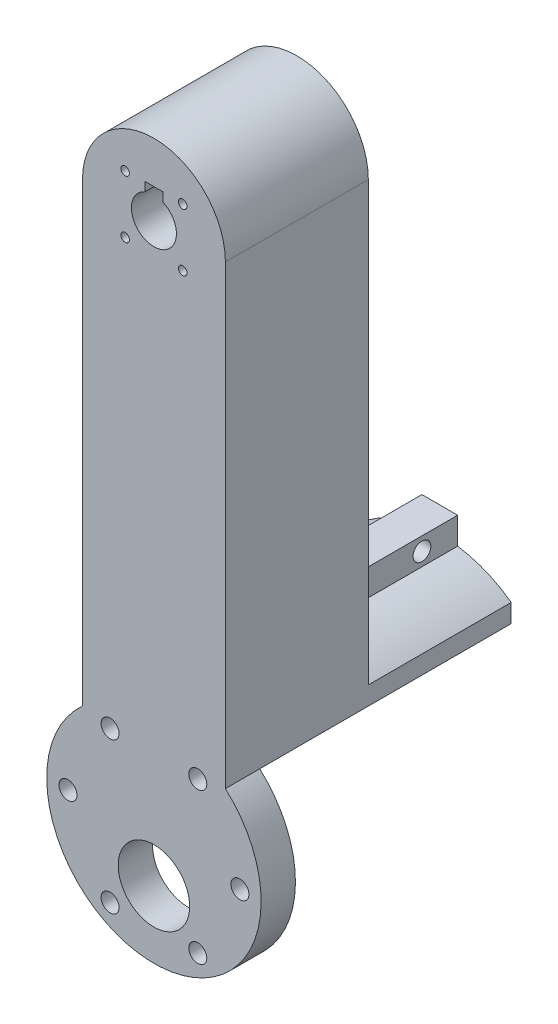
SolidWorks part; units mm, degrees
ref_plane "Front Plane" through (0, 0, 0) normal (0, 0, 1) x (1, 0, 0)
ref_plane "Top Plane" through (0, 0, 0) normal (0, 1, 0) x (1, 0, 0)
ref_plane "Right Plane" through (0, 0, 0) normal (1, 0, 0) x (0, 0, -1)
sketch "Sketch1" plane through (0, 0, 0) normal (0, 0, 1) x (1, 0, 0)
  line L0 (-5.1187, 55.9187) -> (5.1187, 45.6813) construction
  line L2 (12.7, 50.8) -> (12.7, -50.8)
  line L4 (-12.7, 50.8) -> (-12.7, -50.8)
  line L5 (12.7, 50.8) -> (-12.7, -50.8) construction
  line L6 (12.7, -50.8) -> (-12.7, 50.8) construction
  line L7 (5.1187, 55.9187) -> (-5.1187, 45.6813) construction
  line L8 (0, 50.8) -> (0, 51.7208) construction
  arc A0 (-12.7, 50.8) -> (12.7, 50.8) centre (0, 50.8) cw
  arc A1 (12.7, -50.8) -> (-12.7, -50.8) centre (0, -50.8) cw
  circle A2 centre (0, 50.8) radius 4
  circle A3 centre (-5.1187, 55.9187) radius 0.762
  circle A4 centre (5.1187, 55.9187) radius 0.762
  circle A5 centre (5.1187, 45.6813) radius 0.762
  circle A6 centre (-5.1187, 45.6813) radius 0.762
  point P0 (0, 0)
  point P14 (0, 50.8)
  point P15 (0, 50.8)
  dimension "D3" = 8
  dimension "D6" = 1.524
  dimension "D1" = 25.4
  dimension "D2" = 101.6
  dimension "D4" = 45
  dimension "D5" = 14.478
extrude "Boss-Extrude1" add sketch "Sketch1" along normal blind 25.4
sketch "Sketch2" plane through (0, 0, 0) normal (0, 0, -1) x (-1, 0, 0)
  circle A0 centre (0, -44.45) radius 19.05
  arc A2 (-12.7, -50.8) -> (12.7, -50.8) centre (0, -50.8) ccw construction
  dimension "D1" = 38.1
extrude "Boss-Extrude2" add sketch "Sketch2" against normal blind 25.4
sketch "Sketch4" plane through (0, 0, 25.4) normal (0, 0, 1) x (1, 0, 0)
  circle A0 centre (0, -44.45) radius 19.05
  arc A1 (-12.7, -30.251) -> (12.7, -30.251) centre (0, -44.45) ccw construction
  dimension "D1" = 38.1
sketch "Sketch5" plane through (0, 0, 25.4) normal (0, 0, 1) x (1, 0, 0)
  circle A0 centre (0, -51.562) radius 6.35
  dimension "D1" = 12.7
  dimension "D2" = 7.112
extrude "Cut-Extrude2" cut sketch "Sketch5" against normal blind 25.4
sketch "Sketch3" plane through (0, 0, 25.4) normal (0, 0, 1) x (1, 0, 0)
  circle A7 centre (15.2766, -44.45) radius 1.6 construction
  circle A8 centre (0, -44.45) radius 18.5
  circle A9 centre (0, -44.45) radius 18.5
  circle A10 centre (7.7942, -58.0175) radius 1.6 construction
  circle A11 centre (-7.7942, -58.0175) radius 1.6 construction
  circle A12 centre (-15.2766, -44.45) radius 1.6 construction
  circle A13 centre (7.7942, -31.2359) radius 1.6 construction
  circle A14 centre (-7.7942, -31.2359) radius 1.6 construction
  circle A15 centre (15.2766, -44.45) radius 1.6
  circle A16 centre (7.7942, -58.0175) radius 1.6
  circle A17 centre (-7.7942, -58.0175) radius 1.6
  circle A18 centre (-15.2766, -44.45) radius 1.6
  circle A19 centre (7.7942, -31.2359) radius 1.6
  circle A20 centre (-7.7942, -31.2359) radius 1.6
  dimension "D1" = 0
extrude "Cut-Extrude1" cut sketch "Sketch3" against normal blind 25.4 contours A20 | A18 | A15 | A17 | A19 | A16
sketch "Sketch6" plane through (0, 0, 0) normal (0, 0, -1) x (-1, 0, 0)
  line L1 (-1.5875, 56.059) -> (1.5875, 56.059)
  line L2 (-1.5875, 56.059) -> (-1.5875, 54.4715)
  line L3 (-1.5875, 54.4715) -> (1.5875, 54.4715)
  line L4 (1.5875, 56.059) -> (1.5875, 54.4715)
  circle A0 centre (0, 50.8) radius 4 construction
  dimension "D1" = 3.175
  dimension "D2" = 1.5875
extrude "Cut-Extrude3" cut sketch "Sketch6" against normal blind 25.4
sketch "Sketch8" plane through (0, 0, 0) normal (0, 0, -1) x (-1, 0, 0)
  circle A0 centre (0, -44.45) radius 19.05
  dimension "D1" = 38.1
extrude "Cut-Extrude4" cut sketch "Sketch8" against normal blind 19.3
sketch "Sketch9" plane through (0, 0, 0) normal (0, 0, -1) x (-1, 0, 0)
  line L0 (12.7, 50.8) -> (12.7, -30.251) construction
  line L1 (-12.7, -30.251) -> (-12.7, 50.8) construction
  line L2 (-12.7, -30.251) -> (-12.7, -26.9904)
  line L3 (12.7, -30.251) -> (12.7, -26.9904)
  arc A0 (-12.7, -30.251) -> (12.7, -30.251) centre (0, -44.45) cw
  arc A1 (-12.7, -26.9904) -> (12.7, -26.9904) centre (0, -44.45) cw
  dimension "D1" = 2.54
extrude "Boss-Extrude3" add sketch "Sketch9" along normal blind 25.4
sketch "Sketch10" plane through (0, 0, 0) normal (0, 0, -1) x (-1, 0, 0)
  line L1 (-3.175, -18.3322) -> (3.175, -18.3322)
  line L2 (-3.175, -18.3322) -> (-3.175, -23.0947)
  line L3 (-3.175, -23.0947) -> (3.175, -23.0947)
  line L4 (3.175, -18.3322) -> (3.175, -23.0947)
  arc A0 (12.7, -26.9904) -> (-12.7, -26.9904) centre (0, -44.45) ccw construction
  point P4 (0, -18.3322)
  dimension "D1" = 6.35
  dimension "D2" = 4.7625
extrude "Boss-Extrude4" add sketch "Sketch10" along normal up to surface (25.4 mm away) up to face at (0, -26.3753, -25.4)
sketch "Sketch11" plane through (3.175, 0, 0) normal (1, 0, 0) x (0, 0, -1)
  line L0 (24.0343, -18.3322) -> (24.0343, -23.0947) construction
  line L1 (25.4, -18.3322) -> (0, -18.3322) construction
  line L2 (25.4, -23.0947) -> (0, -23.0947) construction
  line L3 (0, -26.9904) -> (0, 50.8) construction
  line L4 (25.4, -23.0947) -> (25.4, -18.3322) construction
  circle A0 centre (6.35, -20.7135) radius 1.5875
  circle A1 centre (19.05, -20.7135) radius 1.5875
  point P9 (24.0343, -20.7135)
  dimension "D1" = 3.175
  dimension "D2" = 6.35
  dimension "D3" = 6.35
extrude "Cut-Extrude5" cut sketch "Sketch11" against normal through all
